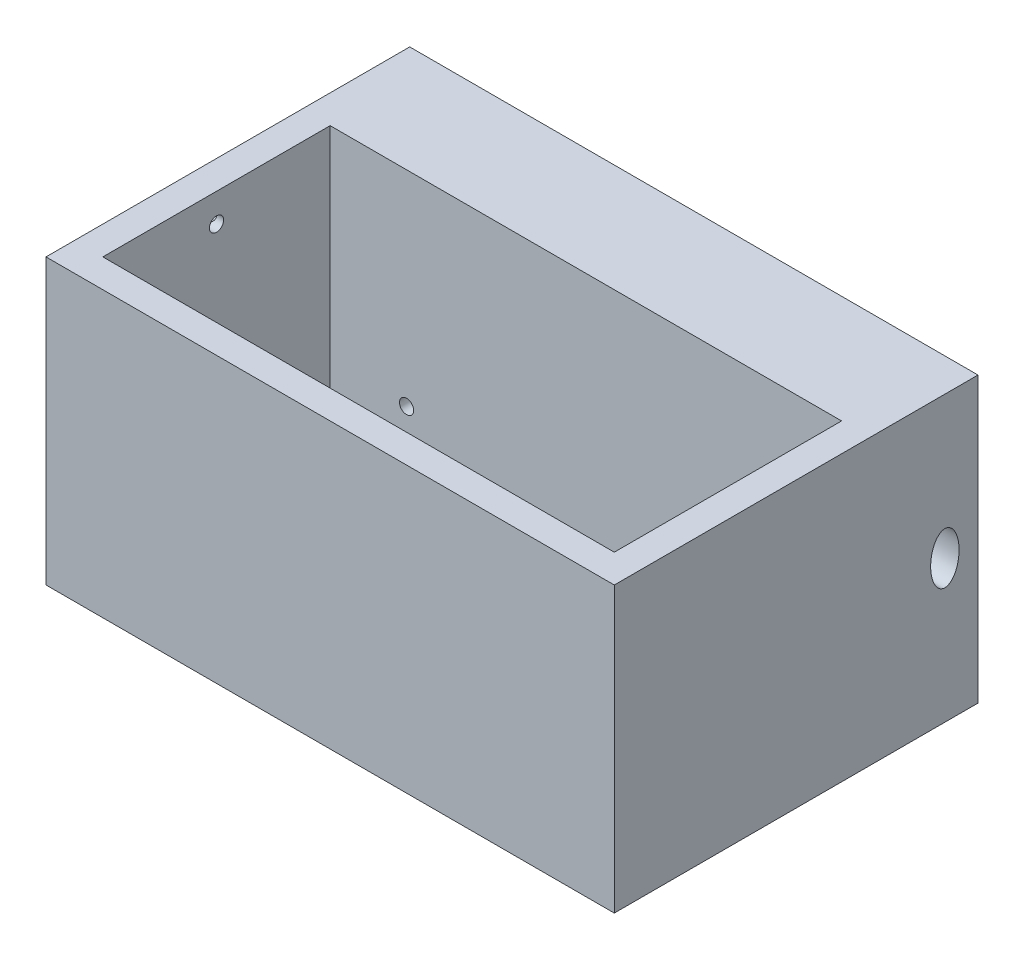
SolidWorks part; units mm, degrees
ref_plane "Front Plane" through (0, 0, 0) normal (0, 0, 1) x (1, 0, 0)
ref_plane "Top Plane" through (0, 0, 0) normal (0, 1, 0) x (1, 0, 0)
ref_plane "Right Plane" through (0, 0, 0) normal (1, 0, 0) x (0, 0, -1)
sketch "Sketch1" plane through (0, 0, 0) normal (0, 1, 0) x (1, 0, 0)
  line L1 (-50, -25) -> (50, -25)
  line L2 (-50, -25) -> (-50, 25)
  line L3 (-50, 25) -> (50, 25)
  line L4 (50, -25) -> (50, 25)
  line L5 (-50, -25) -> (50, 25) construction
  line L6 (-50, 25) -> (50, -25) construction
  point P0 (0, 0)
  dimension "D1" = 100
  dimension "D2" = 50
extrude "Boss-Extrude1" add sketch "Sketch1" along normal blind 50
shell "Shell1" thickness 5
sketch "Sketch5" plane through (-45, 0, 0) normal (1, 0, 0) x (0, 0, -1)
  line L0 (20, 50) -> (-20, 50) construction
  circle A0 centre (0, 45) radius 1.25
  dimension "D1" = 2.5
  dimension "D2" = 5
sketch "Sketch6" plane through (0, 0, 0) normal (0, 1, 0) x (1, 0, 0)
  line L0 (-45, 0) -> (-47.5, 0)
  line L1 (-45, -1.25) -> (-45, 1.25) construction
  line L2 (-47.5, 0) -> (-47.5, 22.5)
  line L3 (-47.5, 22.5) -> (47.5, 22.5)
  line L4 (47.5, 22.5) -> (47.5, -22.5)
  line L5 (47.5, -22.5) -> (-3.75, -22.5)
  line L6 (45, 20) -> (-45, 20) construction
  line L7 (45, -20) -> (45, 20) construction
  line L8 (-50, -25) -> (50, -25) construction
  dimension "D1" = 2.5
  dimension "D2" = 2.5
  dimension "D3" = 2.5
  dimension "D4" = 2.5
  dimension "D5" = 51.25
sweep "Sweep2" add profiles "Sketch5" path "Sketch6"
combine bodies "Combine1" operation type subtract main body 101 bodies to subtract 104
sketch "Sketch7" plane through (0, 5, 0) normal (0, 1, 0) x (1, 0, 0)
  line L0 (-50, -25) -> (50, -25) construction
  line L1 (-50, 25) -> (-50, -25) construction
  circle A0 centre (1.25, -22.5) radius 1.25
  dimension "D1" = 2.5
  dimension "D2" = 2.5
  dimension "D3" = 51.25
ref_plane "Plane1" through (0, 0, 22.5) normal (0, 0, 1) x (1, 0, 0)
sketch "Sketch9" plane through (0, 0, 22.5) normal (0, 0, 1) x (1, 0, 0)
  line L0 (1.25, 0) -> (1.25, 47.5)
  line L1 (-50, 50) -> (50, 50) construction
  line L3 (-50, 0) -> (50, 0) construction
  dimension "D1" = 0
  dimension "D2" = 2.5
sweep "Cut-Sweep1" cut profiles "Sketch7" path "Sketch9"
sketch "Sketch11" plane through (0, 0, 0) normal (0, -1, 0) x (1, 0, 0)
  circle A0 centre (1.25, 22.5) radius 1.25
  dimension "D1" = 2.5
extrude "Cut-Extrude2" cut sketch "Sketch11" against normal blind 5
sketch "Sketch12" plane through (0, 0, -25) normal (0, 0, -1) x (-1, 0, 0)
  line L0 (50, 50) -> (50, 0) construction
  line L1 (-50, 50) -> (50, 50)
  line L2 (-50, 50) -> (-50, 45)
  line L3 (-50, 45) -> (50, 45)
  line L4 (50, 50) -> (50, 45)
  line L5 (-50, 0) -> (50, 0) construction
  line L6 (50, 50) -> (45, 50)
  line L7 (50, 50) -> (50, 0)
  line L8 (50, 0) -> (45, 0)
  line L9 (45, 50) -> (45, 0)
  line L10 (-50, 50) -> (-50, 0) construction
  line L11 (-50, 0) -> (50, 0)
  line L12 (-50, 0) -> (-50, 5)
  line L13 (-50, 5) -> (50, 5)
  line L14 (50, 0) -> (50, 5)
  line L16 (-50, 50) -> (-45, 50)
  line L17 (-50, 50) -> (-50, 0)
  line L18 (-50, 0) -> (-45, 0)
  line L19 (-45, 50) -> (-45, 0)
  line M10 (-50, 0) -> (50, 0)
  line M11 (50, 0) -> (50, 50)
  line M12 (50, 50) -> (-50, 50)
  line M13 (-50, 50) -> (-50, 0)
  dimension "D1" = 5
  dimension "D2" = 5
  dimension "D3" = 0
  dimension "D4" = 5
  dimension "D5" = 5
extrude "Boss-Extrude3" add sketch "Sketch12" along normal blind 14 contours L19 L3 M12 M13 | L1 L19 L3 L9 | L19 L3 L13 M13 | L19 L13 M13 M10 | L13 L19 L11 L9 | L9 L13 L7 L3 | L13 L9 M10 M11 | L9 L3 M12 M11
ref_plane "Plane2" through (-40, 0, 0) normal (-1, 0, 0) x (0, 0, 1)
ref_plane "Plane3" through (0, 0, -35) normal (0, 0, -1) x (-1, 0, 0)
sketch "Sketch17" plane through (0, 0, -39) normal (0, 0, -1) x (-1, 0, 0)
  line L0 (-50, 50) -> (-50, 0) construction
  line L1 (50, 50) -> (-50, 50) construction
  line L2 (50, 0) -> (50, 50) construction
  line L3 (-50, 0) -> (50, 0) construction
  circle A0 centre (-47, 47) radius 2
  circle A1 centre (47, 47) radius 2
  circle A2 centre (47, 3) radius 2
  circle A3 centre (-47, 3) radius 2
  point P16 (0, 0)
  point P18 (-45.2074, 0.4719)
  dimension "D1" = 4
  dimension "D6" = 4
  dimension "D7" = 4
  dimension "D10" = 4
  dimension "D2" = 3
  dimension "D3" = 3
  dimension "D4" = 3
  dimension "D5" = 3
  dimension "D8" = 3
  dimension "D9" = 3
  dimension "D11" = 3
  dimension "D12" = 3
extrude "Cut-Extrude4" cut sketch "Sketch17" against normal blind 5
sketch "Sketch20" plane through (0, 0, -25) normal (0, 0, -1) x (-1, 0, 0)
  circle A0 centre (31.5505, 8.3355) radius 1.25
  dimension "D1" = 2.5
extrude "Cut-Extrude5" cut sketch "Sketch20" against normal up to surface (5 mm away) up to face at (0, 27.5, -20)
sketch "Sketch21" plane through (0, 0, -25) normal (0, 0, -1) x (-1, 0, 0)
  line L0 (-45, 45) -> (-45, 5) construction
  line L1 (-45, 26.8946) -> (45, 26.8946)
  line L2 (-45, 26.8946) -> (-45, 5)
  line L3 (-45, 5) -> (45, 5)
  line L4 (45, 26.8946) -> (45, 5)
  point P6 (-45, 26.8946)
extrude "Cut-Extrude6" cut sketch "Sketch21" against normal blind 2.5
pattern_linear "LPattern2" count 2 spacing 5.6 along (0, 1, 0) of "Cut-Extrude5"
sketch "Sketch22" plane through (-50, 0, 0) normal (-1, 0, 0) x (0, 0, 1)
  line L0 (-20, 9.5855) -> (-22.5, 9.5855) construction
  circle A0 centre (-15.8565, 8.3355) radius 1.25
  dimension "D1" = 2.5
  dimension "D2" = 1.25
extrude "Cut-Extrude7" cut sketch "Sketch22" against normal up to surface (5 mm away) up to face at (-45, 45, -1.25)
sketch "Sketch23" plane through (50, 0, 0) normal (1, 0, 0) x (0, 0, -1)
  line L1 (-25, 0) -> (39, 0) construction
  ellipse E0 centre (33.1692, 25) end of major axis (33.1692, 29.5) minor radius 2.5
  point P1 (33.1692, 25)
  point P10 (0, 0)
  point P11 (0, 0)
  dimension "D1" = 5
  dimension "D3" = 25
extrude "Cut-Extrude8" cut sketch "Sketch23" against normal up to surface (5 mm away) up to face at (45, 25.6315, -28.8333)
